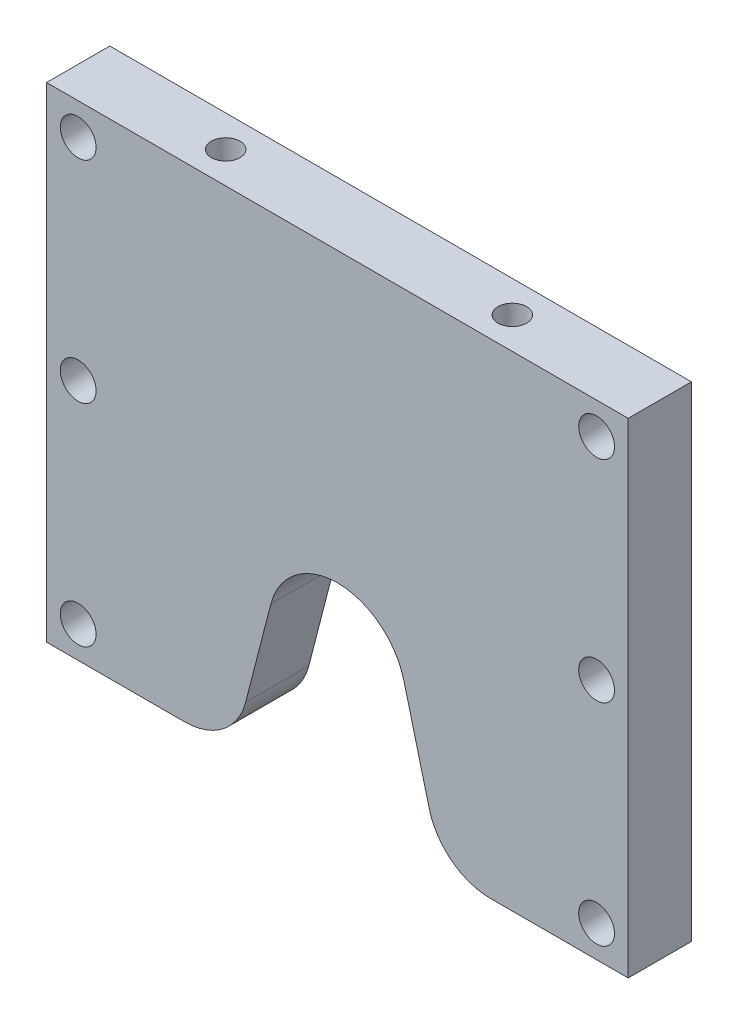
SolidWorks part; units mm, degrees
ref_plane "Alzado" through (0, 0, 0) normal (0, 0, 1) x (1, 0, 0)
ref_plane "Planta" through (0, 0, 0) normal (0, 1, 0) x (1, 0, 0)
ref_plane "Vista lateral" through (0, 0, 0) normal (1, 0, 0) x (0, 0, -1)
sketch "Croquis1" plane through (0, 0, 0) normal (0, 0, 1) x (1, 0, 0)
  line L0 (0, -27.1) -> (0, -57.5) construction
  line L1 (69, -57.5) -> (36.3, -57.5)
  line L2 (69, -57.5) -> (69, 57.5)
  line L3 (69, 57.5) -> (-69, 57.5)
  line L4 (-69, -57.5) -> (-69, 57.5)
  line L5 (69, -57.5) -> (-69, 57.5) construction
  line L6 (69, 57.5) -> (-69, -57.5) construction
  line L7 (-15.7829, -23.0268) -> (-21.7759, -46.2484)
  line L8 (-36.3, -57.5) -> (-69, -57.5)
  line L9 (0, 0) -> (0, -27.1) construction
  line L10 (15.7829, -23.0268) -> (21.7759, -46.2484)
  arc A0 (15.7829, -23.0268) -> (-15.7829, -23.0268) centre (0, -27.1) ccw
  arc A1 (-36.3, -57.5) -> (-21.7759, -46.2484) centre (-36.3, -42.5) ccw
  arc A2 (36.3, -57.5) -> (21.7759, -46.2484) centre (36.3, -42.5) cw
  circle A3 centre (-61.5, 50) radius 4.25
  circle A4 centre (-61.5, 0) radius 4.25
  circle A5 centre (-61.5, -50) radius 4.25
  circle A6 centre (61.5, 50) radius 4.25
  circle A7 centre (61.5, 0) radius 4.25
  circle A8 centre (61.5, -50) radius 4.25
  point P0 (0, 0)
  dimension "D4" = 32.6
  dimension "D7" = 30
  dimension "D5" = 8.5
  dimension "D1" = 138
  dimension "D2" = 115
  dimension "D3" = 30.4
  dimension "D6" = 32.7
  dimension "D8" = 7.5
  dimension "D9" = 7.5
  dimension "D10" = 7.5
  dimension "D11" = 7.5
  dimension "D12" = 50
  dimension "D13" = 50
extrude "Saliente-Extruir1" add sketch "Croquis1" along normal mid plane 15
sketch "Croquis2" plane through (0, 0, -7.5) normal (0, 0, -1) x (-1, 0, 0)
  circle A0 centre (-61.5, 50) radius 6.5
  circle A1 centre (-61.5, 0) radius 6.5
  circle A2 centre (-61.5, -50) radius 6.5
  circle A3 centre (61.5, 50) radius 6.5
  circle A4 centre (61.5, 0) radius 6.5
  circle A5 centre (61.5, -50) radius 6.5
  dimension "D1" = 13
extrude "Cortar-Extruir1" cut sketch "Croquis2" against normal blind 8
hole_wizard "Taladro roscado M81" positions "Croquis4" profile "Croquis3" tap size "M8" standard "DIN"
sketch "Croquis4" plane through (0, 57.5, 0) normal (0, 1, 0) x (-1, 0, 0)
  line L0 (69, 7.5) -> (69, -7.5) construction
  line L1 (-69, 7.5) -> (-69, -7.5) construction
  line L2 (-69, -7.5) -> (69, -7.5) construction
  line L3 (-69, 7.5) -> (69, 7.5) construction
  point P0 (34, 0)
  point P4 (-34, 0)
  dimension "D1" = 35
  dimension "D2" = 35
  dimension "D3" = 7.5
  dimension "D4" = 7.5
sketch "Croquis3" plane through (-34, 57.5, 0) normal (1, 0, 0) x (0, 0, 1)
  line L0 (0, 0) -> (0, 22.0429)
  line L1 (0, 22.0429) -> (3.4, 20)
  line L2 (3.4, 20) -> (3.4, 0)
  line L5 (3.4, 0) -> (0, 0)
  line L10 (0, 22.0429) -> (-3.4, 20) construction
  line L11 (0, -6.35) -> (0, 107.95) construction
  dimension "Diámetro de perforador para roscar" = 6.8
  dimension "Profundidad de perforador para roscar" = 20
  dimension "Ángulo de perforador" = 118
cosmetic thread "Rosca de taladro1" parameters "D1"=16, "D2"=8
cosmetic thread "Rosca de taladro2" parameters "D1"=16, "D2"=8
